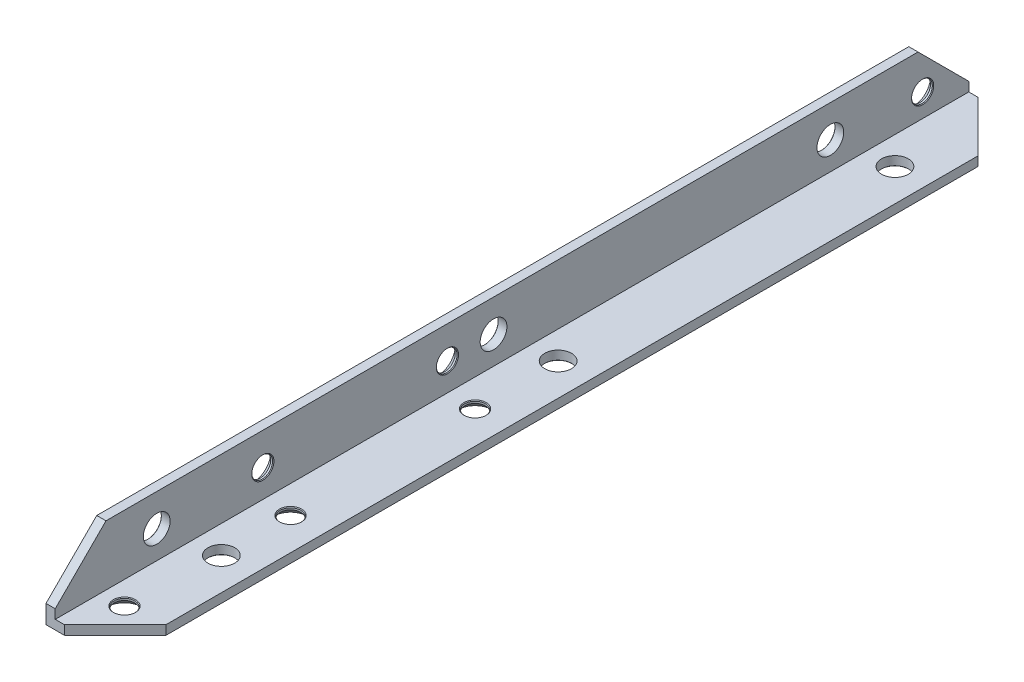
SolidWorks part; units mm, degrees
ref_plane "Спереди" through (0, 0, 0) normal (0, 0, 1) x (1, 0, 0)
ref_plane "Сверху" through (0, 0, 0) normal (0, 1, 0) x (1, 0, 0)
ref_plane "Справа" through (0, 0, 0) normal (1, 0, 0) x (0, 0, -1)
sketch "Эскиз1" plane through (0, 0, 0) normal (0, 0, 1) x (1, 0, 0)
  line L0 (0, 0) -> (0, 15)
  line L1 (0, 15) -> (2, 15)
  line L2 (2, 15) -> (2, 2)
  line L3 (2, 2) -> (15, 2)
  line L4 (15, 2) -> (15, 0)
  line L5 (15, 0) -> (0, 0)
  dimension "D1" = 2
  dimension "D2" = 15
extrude "Бобышка-Вытянуть1" add sketch "Эскиз1" along normal blind 198
chamfer "Фаска1" distance 11 angle 45 4 edges at (1, 15, 0) (15, 1, 0) (15, 1, 198) (1, 15, 198)
hole_wizard "Зенковка для винта с потайной головкой M41" positions "Эскиз3" profile "Эскиз2" countersink size "M4" standard "DIN" end condition through all
sketch "Эскиз3" plane through (0, 0, 0) normal (0, -1, 0) x (1, 0, 0)
  line L0 (0, 198) -> (0, 0) construction
  line L1 (0, 198) -> (4, 198) construction
  point P1 (7, 188)
  point P11 (8, 153)
  point P13 (8, 113)
  dimension "D1" = 7
  dimension "D2" = 10
  dimension "D3" = 35
  dimension "D4" = 40
  dimension "D5" = 1
sketch "Эскиз2" plane through (7, 0, 188) normal (1, 0, 0) x (0, 0, -1)
  line L0 (0, 0) -> (0, 2)
  line L1 (0, 2) -> (2.4, 2)
  line L2 (2.25, 1.85) -> (2.25, 1.45)
  line L3 (2.25, 1.45) -> (3.7, 0)
  line L5 (3.7, 0) -> (0, 0)
  line L6 (-2.25, 1.45) -> (-3.7, 0) construction
  line L7 (2.4, 2) -> (2.25, 1.85)
  line L8 (-2.4, 2) -> (-2.25, 1.85) construction
  line L11 (0, -6.35) -> (0, 107.95) construction
  dimension "Диаметр сквозного отверстия" = 4.5
  dimension "Глубина сквозного отверстия" = 2
  dimension "Диаметр передней зенковки" = 7.4
  dimension "Угол передней зенковки" = 90
  dimension "Диаметр задней зенковки" = 4.8
  dimension "Угол задней зенковки" = 90
hole_wizard "Зенковка для винта с потайной головкой M42" positions "Эскиз5" profile "Эскиз4" countersink size "M4" standard "DIN" end condition through all
sketch "Эскиз5" plane through (0, 0, 0) normal (-1, 0, 0) x (0, 0, 1)
  line L0 (0, 4) -> (0, 0) construction
  line L2 (198, 0) -> (0, 0) construction
  point P0 (10, 7)
  point P12 (113, 8)
  point P14 (153, 8)
  dimension "D5" = 103
  dimension "D1" = 10
  dimension "D2" = 1
  dimension "D3" = 7
  dimension "D4" = 40
sketch "Эскиз4" plane through (0, 7, 10) normal (0, 1, 0) x (0, 0, 1)
  line L0 (0, 0) -> (0, 2)
  line L1 (0, 2) -> (2.4, 2)
  line L2 (2.25, 1.85) -> (2.25, 1.45)
  line L3 (2.25, 1.45) -> (3.7, 0)
  line L5 (3.7, 0) -> (0, 0)
  line L6 (-2.25, 1.45) -> (-3.7, 0) construction
  line L7 (2.4, 2) -> (2.25, 1.85)
  line L8 (-2.4, 2) -> (-2.25, 1.85) construction
  line L11 (0, -6.35) -> (0, 107.95) construction
  dimension "Диаметр сквозного отверстия" = 4.5
  dimension "Глубина сквозного отверстия" = 2
  dimension "Диаметр передней зенковки" = 7.4
  dimension "Угол передней зенковки" = 90
  dimension "Диаметр задней зенковки" = 4.8
  dimension "Угол задней зенковки" = 90
hole_wizard "Отверстие с зазором M51" positions "Эскиз7" profile "Эскиз6" hole size "M5" standard "Ansi (метрические)"
sketch "Эскиз7" plane through (0, 0, 0) normal (-1, 0, 0) x (0, 0, 1)
  line L0 (198, 0) -> (0, 0) construction
  circle A0 centre (10, 7) radius 3.7 construction
  point P1 (103, 8)
  point P10 (30, 8)
  point P12 (176, 8)
  dimension "D1" = 93
  dimension "D2" = 8
  dimension "D3" = 73
  dimension "D4" = 73
sketch "Эскиз6" plane through (0, 8, 103) normal (0, 1, 0) x (0, 0, 1)
  line L0 (0, 0) -> (0, 4.7425)
  line L1 (0, 4.7425) -> (2.9, 3)
  line L2 (2.9, 3) -> (2.9, 0.1)
  line L3 (2.9, 0.1) -> (3, 0)
  line L5 (3, 0) -> (0, 0)
  line L6 (-2.9, 0.1) -> (-3, 0) construction
  line L10 (0, 4.7425) -> (-2.9, 3) construction
  line L11 (0, -6.35) -> (0, 107.95) construction
  dimension "Диаметр отверстия" = 5.8
  dimension "Глубина отверстия" = 3
  dimension "Диаметр передней зенковки" = 6
  dimension "Угол передней зенковки" = 90
  dimension "Угол заточки сверла" = 118
hole_wizard "Отверстие с зазором M52" positions "Эскиз9" profile "Эскиз8" hole size "M5" standard "Ansi (метрические)"
sketch "Эскиз9" plane through (0, 0, 0) normal (0, -1, 0) x (1, 0, 0)
  line L0 (0, 198) -> (0, 0) construction
  circle A0 centre (7, 188) radius 2.25 construction
  point P0 (8, 95)
  point P6 (8, 22)
  point P9 (8, 168)
  dimension "D1" = 8
  dimension "D2" = 93
  dimension "D3" = 73
  dimension "D4" = 73
sketch "Эскиз8" plane through (8, 0, 95) normal (1, 0, 0) x (0, 0, -1)
  line L0 (0, 0) -> (0, 4.7425)
  line L1 (0, 4.7425) -> (2.9, 3)
  line L2 (2.9, 3) -> (2.9, 0.1)
  line L3 (2.9, 0.1) -> (3, 0)
  line L5 (3, 0) -> (0, 0)
  line L6 (-2.9, 0.1) -> (-3, 0) construction
  line L10 (0, 4.7425) -> (-2.9, 3) construction
  line L11 (0, -6.35) -> (0, 107.95) construction
  dimension "Диаметр отверстия" = 5.8
  dimension "Глубина отверстия" = 3
  dimension "Диаметр передней зенковки" = 6
  dimension "Угол передней зенковки" = 90
  dimension "Угол заточки сверла" = 118
